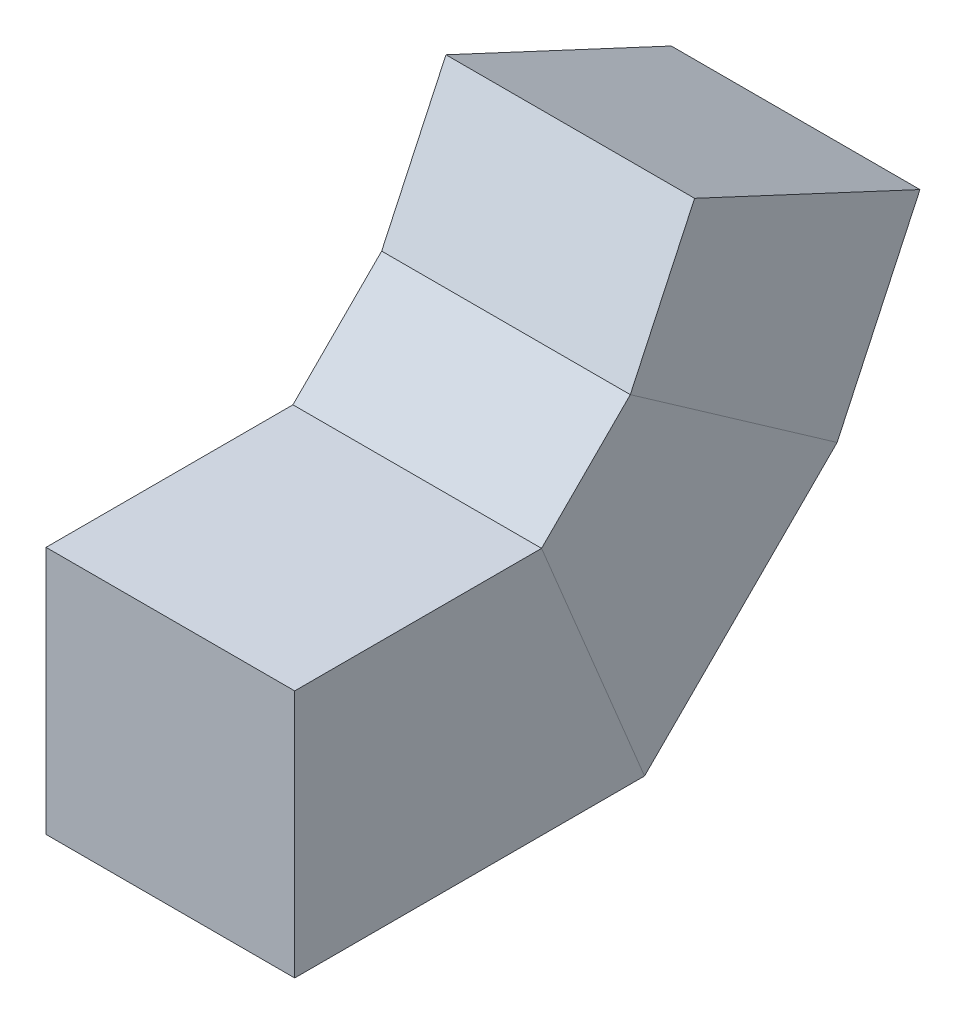
SolidWorks part; units mm, degrees
ref_plane "Front Plane" through (0, 0, 0) normal (0, 0, 1) x (1, 0, 0)
ref_plane "Top Plane" through (0, 0, 0) normal (0, 1, 0) x (1, 0, 0)
ref_plane "Right Plane" through (0, 0, 0) normal (1, 0, 0) x (0, 0, -1)
sketch "Sketch1" plane through (0, 0, 0) normal (0, 0, 1) x (1, 0, 0)
  line L1 (50, 50) -> (-50, 50)
  line L2 (50, 50) -> (50, -50)
  line L3 (50, -50) -> (-50, -50)
  line L4 (-50, 50) -> (-50, -50)
  line L5 (50, 50) -> (-50, -50) construction
  line L6 (50, -50) -> (-50, 50) construction
  point P0 (0, 0)
  dimension "D1" = 100
sketch "Sketch3" plane through (0, 0, 0) normal (1, 0, 0) x (0, 0, -1)
  line L0 (0, 0) -> (120, 0)
  line L1 (0, 50) -> (0, -50) construction
  line L2 (120, 0) -> (176.5685, 56.5685)
  line L3 (176.5685, 56.5685) -> (206.1518, 120.0101)
  point P6 (120, -82.3037)
  point P7 (0, 0)
  point P8 (0, 0)
  point P10 (216.2742, 114.218)
  point P11 (198.798, 122.9451)
  dimension "D1" = 120
  dimension "D2" = 70
  dimension "D3" = 45
  dimension "D4" = 80
  dimension "D5" = 200
sweep "Sweep1" add profiles "Sketch1" path "Sketch3"
